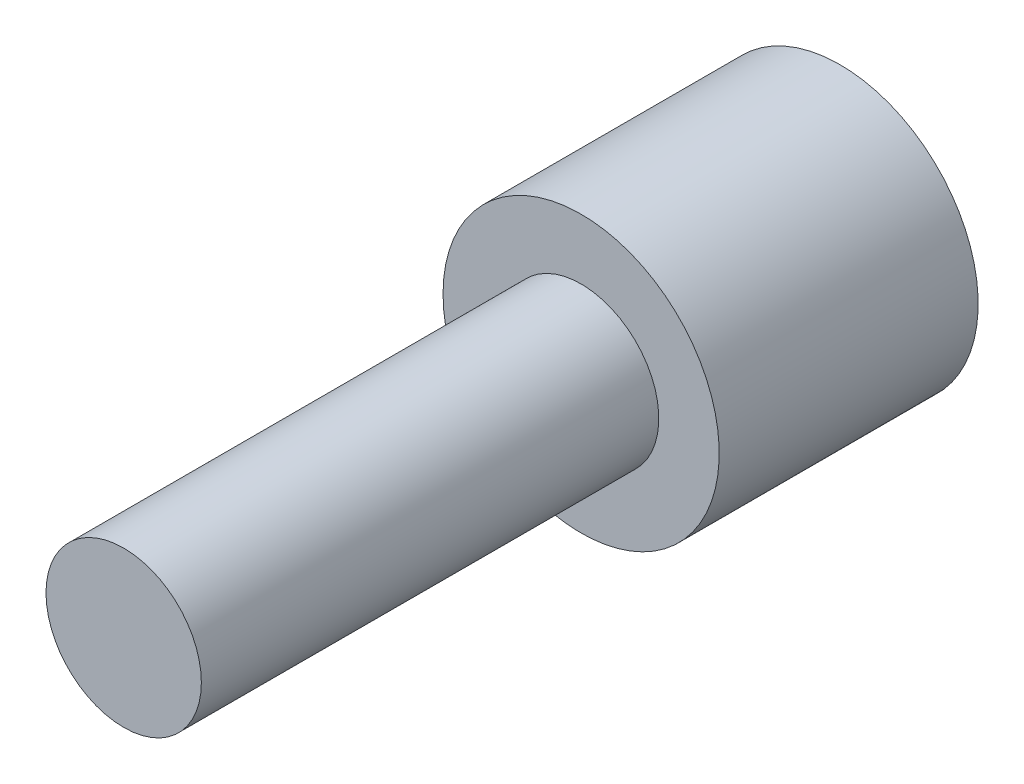
SolidWorks part; units mm, degrees
ref_plane "Front Plane" through (0, 0, 0) normal (0, 0, 1) x (1, 0, 0)
ref_plane "Top Plane" through (0, 0, 0) normal (0, 1, 0) x (1, 0, 0)
ref_plane "Right Plane" through (0, 0, 0) normal (1, 0, 0) x (0, 0, -1)
sketch "Sketch2" plane through (0, 0, 0) normal (0, 0, 1) x (1, 0, 0)
  circle A0 centre (0, 0) radius 1.8
extrude "Boss-Extrude1" add sketch "Sketch2" along normal blind 16.6 contours A0
sketch "Sketch3" plane through (0, 0, 0) normal (0, 0, -1) x (-1, 0, 0)
  circle A0 centre (0, 0) radius 3.2
extrude "Boss-Extrude2" add sketch "Sketch3" against normal blind 6
